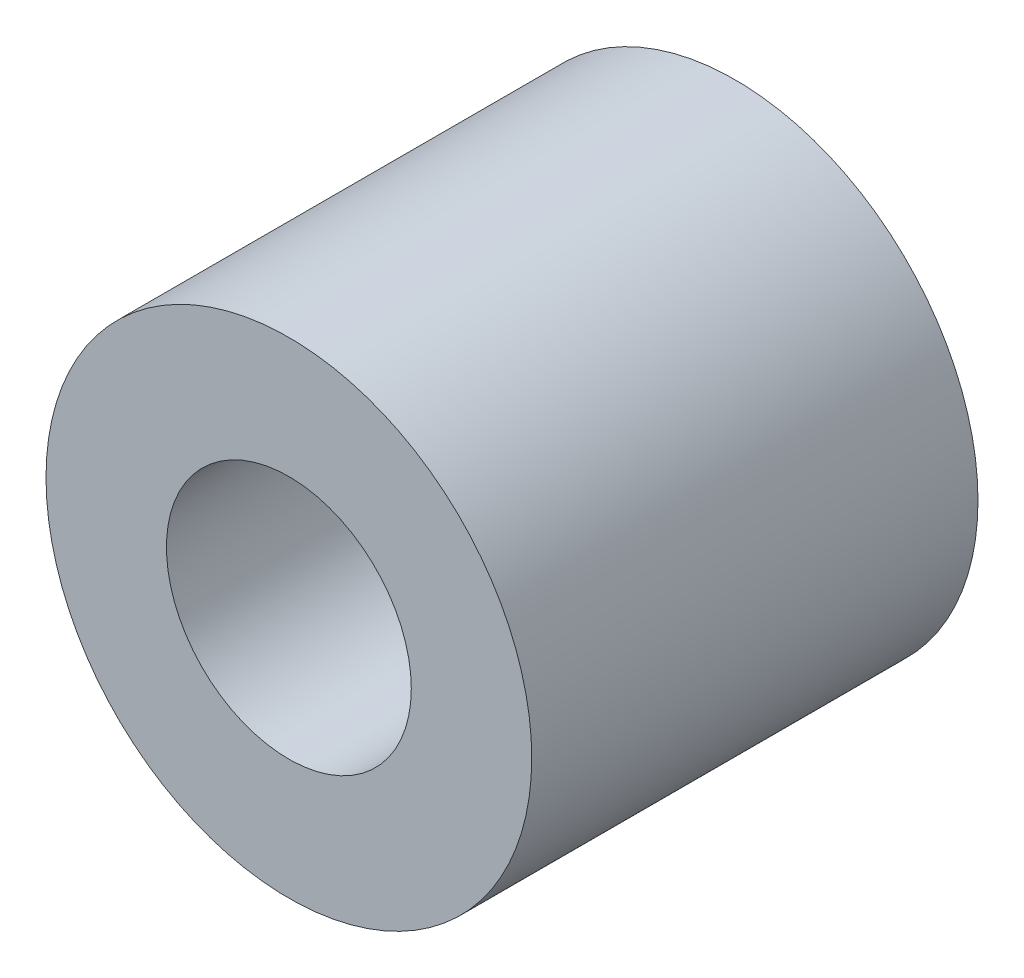
SolidWorks part; units mm, degrees
ref_plane "Front Plane" through (0, 0, 0) normal (0, 0, 1) x (1, 0, 0)
ref_plane "Top Plane" through (0, 0, 0) normal (0, 1, 0) x (1, 0, 0)
ref_plane "Right Plane" through (0, 0, 0) normal (1, 0, 0) x (0, 0, -1)
sketch "Sketch1" plane through (0, 0, 0) normal (0, 0, 1) x (1, 0, 0)
  circle A0 centre (0, 0) radius 3.1242
  circle A1 centre (0, 0) radius 1.5748
  dimension "D1" = 6.2484
  dimension "D2" = 3.1496
extrude "Boss-Extrude1" add sketch "Sketch1" along normal blind 5.7404
